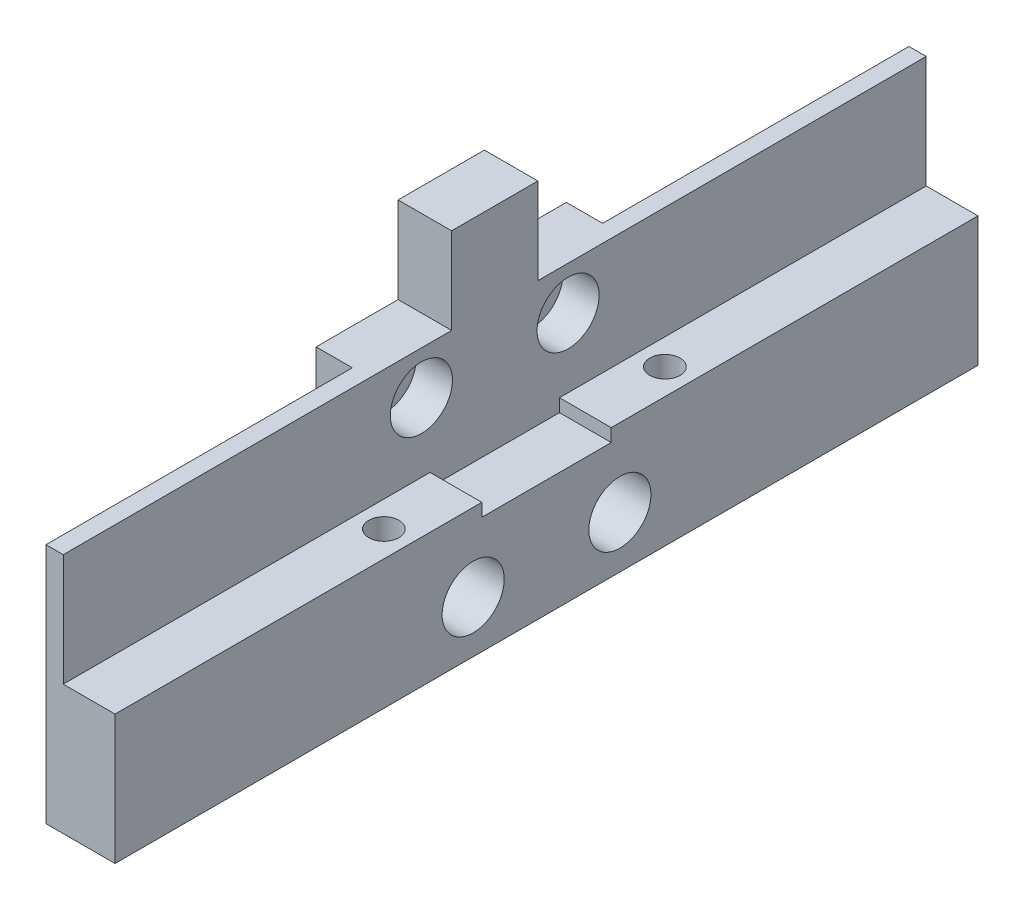
SolidWorks part; units mm, degrees
ref_plane "Front Plane" through (0, 0, 0) normal (0, 0, 1) x (1, 0, 0)
ref_plane "Top Plane" through (0, 0, 0) normal (0, 1, 0) x (1, 0, 0)
ref_plane "Right Plane" through (0, 0, 0) normal (1, 0, 0) x (0, 0, -1)
sketch "Sketch1" plane through (0, 0, 0) normal (1, 0, 0) x (0, 0, -1)
  line L1 (0, 0) -> (100, 0)
  line L2 (0, 0) -> (0, 26)
  line L3 (0, 26) -> (100, 26)
  line L4 (100, 0) -> (100, 26)
  dimension "D1" = 100
  dimension "D2" = 26
extrude "Boss-Extrude1" add sketch "Sketch1" along normal blind 2
sketch "Sketch2" plane through (0, 0, 0) normal (0, 0, 1) x (1, 0, 0)
  line L0 (2, 26) -> (2, 28)
  line L1 (2, 28) -> (-12, 28)
  line L2 (-12, 28) -> (-12, 24)
  line L3 (-12, 24) -> (-10, 24)
  line L4 (-10, 24) -> (-10, 26)
  line L5 (-10, 26) -> (2, 26)
  line L6 (2, 0) -> (0, 0) construction
  line L7 (0, 26) -> (0, 0) construction
  dimension "D1" = 10
  dimension "D2" = 2
extrude "Boss-Extrude2" add sketch "Sketch2" against normal up to surface (100 mm away) up to face at (1, 13, -100)
sketch "Sketch3" plane through (2, 0, 0) normal (1, 0, 0) x (0, 0, -1)
  line L0 (100, 28) -> (0, 28) construction
  line L1 (37.5, 28) -> (62.5, 28)
  line L2 (37.5, 28) -> (37.5, 0)
  line L3 (37.5, 0) -> (62.5, 0)
  line L4 (62.5, 28) -> (62.5, 0)
  line L5 (0, 0) -> (100, 0) construction
  point P8 (50, 0)
  point P9 (50, 28)
  dimension "D1" = 25
  dimension "D2" = 28
extrude "Boss-Extrude3" add sketch "Sketch3" along normal blind 4
sketch "Sketch4" plane through (6, 0, 0) normal (1, 0, 0) x (0, 0, -1)
  line L0 (62.5, 28) -> (37.5, 28) construction
  line L1 (41.5, 21) -> (58.5, 21) construction
  line L2 (41.5, 21) -> (41.5, 4) construction
  line L3 (41.5, 4) -> (58.5, 4) construction
  line L4 (58.5, 21) -> (58.5, 4) construction
  line L5 (37.5, 28) -> (37.5, 0) construction
  line L6 (37.5, 25) -> (62.5, 25) construction
  line L7 (37.5, 25) -> (37.5, 0) construction
  line L8 (37.5, 0) -> (62.5, 0) construction
  line L9 (62.5, 25) -> (62.5, 0) construction
  circle A0 centre (41.5, 21) radius 2.1
  circle A1 centre (58.5, 21) radius 2.1
  circle A2 centre (58.5, 4) radius 2.1
  circle A3 centre (41.5, 4) radius 2.1
  point P6 (50, 28)
  point P7 (50, 21)
  point P15 (62.5, 12.5)
  point P16 (58.5, 12.5)
  dimension "D2" = 25
  dimension "D3" = 4.2
  dimension "D1" = 17
extrude "Cut-Extrude1" cut sketch "Sketch4" against normal through all
mirror "Mirror1" about plane through (6, 0, 0) normal (1, 0, 0) of bodies 104
delete or keep bodies "Body-Delete/Keep 1" type delete bodies bodies 104
sketch "Sketch5" plane through (12, 0, 0) normal (1, 0, 0) x (0, 0, -1)
  line L0 (-10, 36) -> (-10, -10)
  line L1 (-10, -10) -> (110, -10)
  line L2 (110, -10) -> (110, 36)
  line L3 (110, 36) -> (-10, 36)
  line L4 (0, 26) -> (0, 0)
  line L5 (0, 0) -> (100, 0)
  line L6 (100, 0) -> (100, 26)
  line L7 (100, 26) -> (0, 26)
  line L8 (0, 26) -> (0, 0)
  line L9 (0, 0) -> (100, 0)
  line L10 (100, 0) -> (100, 26)
  line L11 (100, 26) -> (0, 26)
  dimension "D1" = 0
  dimension "D2" = 10
extrude "Cut-Extrude2" cut sketch "Sketch5" against normal through all both and the other way through all
sketch "Sketch6" plane through (12, 0, 0) normal (1, 0, 0) x (0, 0, -1)
  line L4 (0, 26) -> (0, 0)
  line L5 (0, 0) -> (100, 0)
  line L6 (100, 0) -> (100, 26)
  line L7 (100, 26) -> (0, 26)
  line L8 (0, 26) -> (0, 0)
  line L9 (0, 0) -> (100, 0)
  line L10 (100, 0) -> (100, 26)
  line L11 (100, 26) -> (0, 26)
  circle A0 centre (41.5, 21) radius 3.6
  circle A1 centre (58.5, 21) radius 3.6
  circle A2 centre (58.5, 4) radius 3.6
  circle A3 centre (41.5, 4) radius 3.6
  dimension "D2" = 7.2
  dimension "D1" = 0
extrude "Boss-Extrude4" add sketch "Sketch6" along normal blind 4.2
sketch "Sketch8" plane through (16.2, 0, 0) normal (1, 0, 0) x (0, 0, -1)
  line L0 (100, 0) -> (100, 26) construction
  line L1 (0, 0) -> (100, 0)
  line L2 (0, 0) -> (0, -4)
  line L3 (0, -4) -> (100, -4)
  line L4 (100, 0) -> (100, -4)
  dimension "D1" = 4
extrude "Boss-Extrude5" add sketch "Sketch8" along normal blind 6 separate body
sketch "Sketch9" plane through (16.2, 0, 0) normal (-1, 0, 0) x (0, 0, 1)
  line L4 (0, -4) -> (0, 0)
  line L5 (0, 0) -> (-100, 0)
  line L6 (-100, 0) -> (-100, -4)
  line L7 (-100, -4) -> (0, -4)
  line L8 (0, -4) -> (0, 0)
  line L9 (0, 0) -> (-100, 0)
  line L10 (-100, 0) -> (-100, -4)
  line L11 (-100, -4) -> (0, -4)
  dimension "D1" = 0
extrude "Boss-Extrude6" add sketch "Sketch9" along normal up to surface (10.2 mm away) up to face at (6, 4, -43.6)
sketch "Sketch10" plane through (0, 0, 0) normal (0, 1, 0) x (1, 0, 0)
  line L4 (6, 0) -> (10, 0)
  line L5 (10, 0) -> (10, 37.5)
  line L6 (10, 37.5) -> (6, 37.5)
  line L7 (6, 37.5) -> (6, 0)
  line L8 (6, 0) -> (10, 0)
  line L9 (10, 0) -> (10, 37.5)
  line L10 (10, 37.5) -> (6, 37.5)
  line L11 (6, 37.5) -> (6, 0)
  line L12 (6, 100) -> (6, 62.5)
  line L13 (6, 62.5) -> (10, 62.5)
  line L14 (10, 62.5) -> (10, 100)
  line L15 (10, 100) -> (6, 100)
  line L16 (6, 100) -> (6, 62.5)
  line L17 (6, 62.5) -> (10, 62.5)
  line L18 (10, 62.5) -> (10, 100)
  line L19 (10, 100) -> (6, 100)
  dimension "D1" = 0
  dimension "D2" = 0
extrude "Cut-Extrude3" cut sketch "Sketch10" against normal through all contours L18 L19 L16 L17 | L11 L8 L9 L10
sketch "Sketch11" plane through (0, 26, 0) normal (0, 1, 0) x (1, 0, 0)
  line L1 (6, 62.5) -> (10, 62.5)
  line L2 (6, 62.5) -> (6, 37.5)
  line L3 (6, 37.5) -> (10, 37.5)
  line L4 (10, 62.5) -> (10, 37.5)
extrude "Cut-Extrude4" cut sketch "Sketch11" against normal through all
sketch "Sketch13" plane through (10, 0, 0) normal (-1, 0, 0) x (0, 0, 1)
  line L0 (-100, 26) -> (0, 26) construction
  line L1 (-55, 26) -> (-45, 26)
  line L2 (-55, 26) -> (-55, 36)
  line L3 (-55, 36) -> (-45, 36)
  line L4 (-45, 26) -> (-45, 36)
  point P6 (-50, 26)
  point P7 (-50, 26)
  dimension "D1" = 10
  dimension "D2" = 10
extrude "Boss-Extrude7" add sketch "Sketch13" against normal up to surface (6.2 mm away) up to face at (16.2, 13, -50)
sketch "Sketch14" plane through (0, 26, 0) normal (0, 1, 0) x (1, 0, 0)
  line L0 (10, 0) -> (16.2, 0) construction
  line L1 (14.2, 0) -> (10, 0)
  line L2 (14.2, 0) -> (14.2, 35.5)
  line L3 (14.2, 35.5) -> (10, 35.5)
  line L4 (10, 0) -> (10, 35.5)
  line L5 (10, 45) -> (10, 0) construction
  line L7 (10, 100) -> (14.2, 100)
  line L8 (10, 100) -> (10, 64.5)
  line L9 (10, 64.5) -> (14.2, 64.5)
  line L10 (14.2, 100) -> (14.2, 64.5)
  dimension "D1" = 29
  dimension "D2" = 2
extrude "Cut-Extrude5" cut sketch "Sketch14" against normal through all
sketch "Sketch15" plane through (22.2, 0, 0) normal (1, 0, 0) x (0, 0, -1)
  line L0 (100, 0) -> (100, 26) construction
  line L1 (0, 0) -> (100, 0)
  line L2 (0, 0) -> (0, 13)
  line L3 (0, 13) -> (42.5, 13)
  line L4 (100, 0) -> (100, 13)
  line L5 (57.5, 13) -> (100, 13)
  line L7 (42.5, 13) -> (42.5, 11.5)
  line L8 (42.5, 11.5) -> (57.5, 11.5)
  line L9 (57.5, 13) -> (57.5, 11.5)
  line L10 (0, -4) -> (100, -4) construction
  line L11 (0, 26) -> (0, 0) construction
  line L12 (42.5, 13) -> (57.5, 13) construction
  circle A0 centre (41.5, 4) radius 3.6 construction
  circle A1 centre (41.5, 4) radius 3.6
  circle A2 centre (58.5, 4) radius 3.6 construction
  circle A3 centre (58.5, 4) radius 3.6
  point P13 (50, -4)
  point P14 (50, 11.5)
  point P17 (0, 13)
  dimension "D1" = 3
  dimension "D2" = 15
extrude "Boss-Extrude8" add sketch "Sketch15" against normal up to surface (6 mm away) up to face at (16.2, 22, -50)
sketch "Sketch17" plane through (0, 13, 0) normal (0, 1, 0) x (1, 0, 0)
  line L0 (22.2, 37.9) -> (22.2, 45.1) construction
  line L1 (22.2, 37.9) -> (22.2, 45.1) construction
  line L2 (15.8496, 50.4334) -> (29.6829, 50.4334) construction
  line L3 (19.2, 0) -> (19.2, 100) construction
  line L4 (16.2, 0) -> (22.2, 0) construction
  line L5 (16.2, 100) -> (22.2, 100) construction
  line L6 (22.2, 37.9) -> (16.2, 37.9) construction
  line L7 (16.2, 0) -> (16.2, 42.5) construction
  circle A0 centre (19.2, 34.15) radius 1.75
  circle A1 centre (19.2, 66.7168) radius 1.75
  dimension "D1" = 3.5
  dimension "D2" = 2
extrude "Cut-Extrude7" cut sketch "Sketch17" against normal through all
other "Move Face2" face at (19.2, -4, -32.4) parameters "D1"=2
